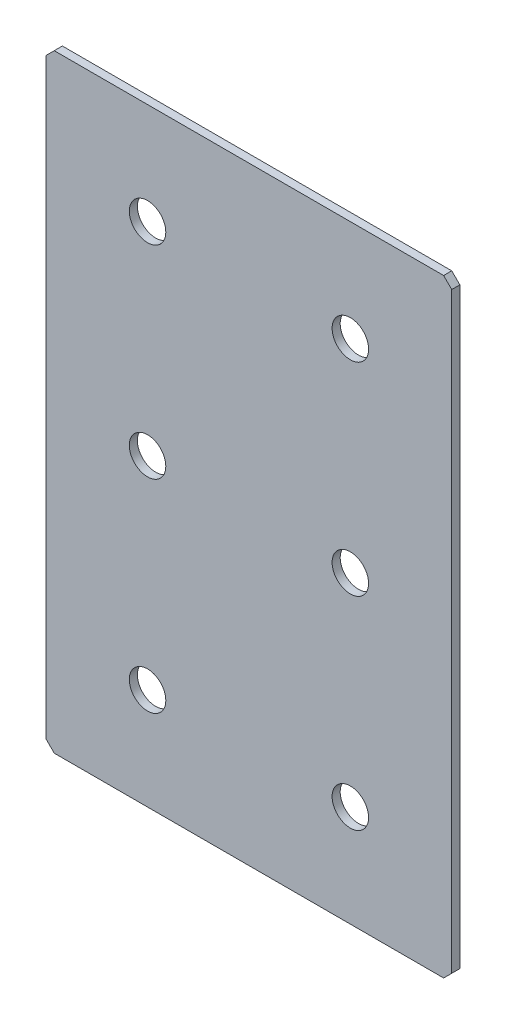
SolidWorks part; units mm, degrees
material "Простая углеродистая сталь"
ref_plane "Спереди(Плоскость XY)" through (0, 0, 0) normal (0, 0, 1) x (1, 0, 0)
ref_plane "Сверху(Плоскость XZ)" through (0, 0, 0) normal (0, 1, 0) x (1, 0, 0)
ref_plane "Справа(Плоскость ZY)" through (0, 0, 0) normal (1, 0, 0) x (0, 0, -1)
sketch "Эскиз1" plane through (0, 0, 0) normal (0, 0, 1) x (1, 0, 0)
  line L1 (-50, -75) -> (50, -75)
  line L2 (-50, -75) -> (-50, 75)
  line L3 (-50, 75) -> (50, 75)
  line L4 (50, -75) -> (50, 75)
  line L5 (-50, -75) -> (50, 75) construction
  line L6 (-50, 75) -> (50, -75) construction
  point P0 (0, 0)
  dimension "D1" = 100
  dimension "D2" = 150
extrude "Бобышка-Вытянуть1" add sketch "Эскиз1" along normal blind 2
chamfer "Фаска1" distance 2 angle 45 4 edges at (-50, -75, 1) (50, -75, 1) (-50, 75, 1) (50, 75, 1)
hole_wizard "Отверстие с зазором M81" positions "Эскиз2" profile "Эскиз3" hole size "M8" standard "DIN" end condition through all
sketch "Эскиз2" plane through (0, 0, 2) normal (0, 0, 1) x (1, 0, 0)
  line L0 (-25, 0) -> (25, 0) construction
  line L1 (25, 0) -> (25, 50) construction
  line L3 (25, 0) -> (25, -50) construction
  line L5 (-25, 0) -> (-25, 50) construction
  line L7 (-25, 0) -> (-25, -50) construction
  point P0 (-25, 50)
  point P2 (25, 50)
  point P4 (25, 0)
  point P6 (-25, 0)
  point P8 (-25, -50)
  point P10 (25, -50)
  dimension "D1" = 50
sketch "Эскиз3" plane through (-25, 50, 2) normal (1, 0, 0) x (0, -1, 0)
  line L0 (0, 0) -> (0, 2)
  line L1 (0, 2) -> (4.5, 2)
  line L2 (4.5, 2) -> (4.5, 0)
  line L5 (4.5, 0) -> (0, 0)
  line L11 (0, -6.35) -> (0, 107.95) construction
  dimension "Диаметр сквозного отверстия" = 9
  dimension "Глубина сквозного отверстия" = 2
